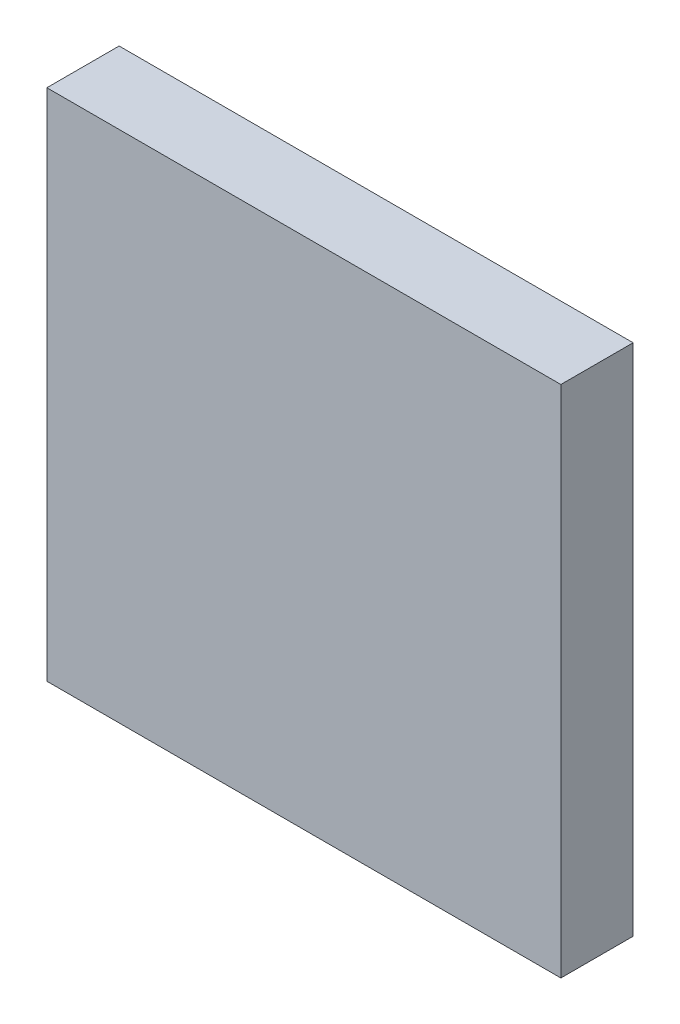
SolidWorks part; units mm, degrees
ref_plane "Front Plane" through (0, 0, 0) normal (0, 0, 1) x (1, 0, 0)
ref_plane "Top Plane" through (0, 0, 0) normal (0, 1, 0) x (1, 0, 0)
ref_plane "Right Plane" through (0, 0, 0) normal (1, 0, 0) x (0, 0, -1)
sketch "Sketch1" plane through (0, 0, 0) normal (0, 0, 1) x (1, 0, 0)
  line L0 (-3.556, 3.556) -> (3.556, 3.556)
  line L1 (3.556, 3.556) -> (3.556, -3.556)
  line L2 (3.556, -3.556) -> (-3.556, -3.556)
  line L3 (-3.556, -3.556) -> (-3.556, 3.556)
extrude "Component_Outline" add sketch "Sketch1" along normal blind 1 separate body
sketch3d "3DSketch1"
  line L0 (0, 0, 0) -> (1, 0, 0)
  line L1 (0, 0, 0) -> (0, 1, 0)
  line L2 (0, 0, 0) -> (0, 0, 1)
  point P0 (0, 0, 0)
